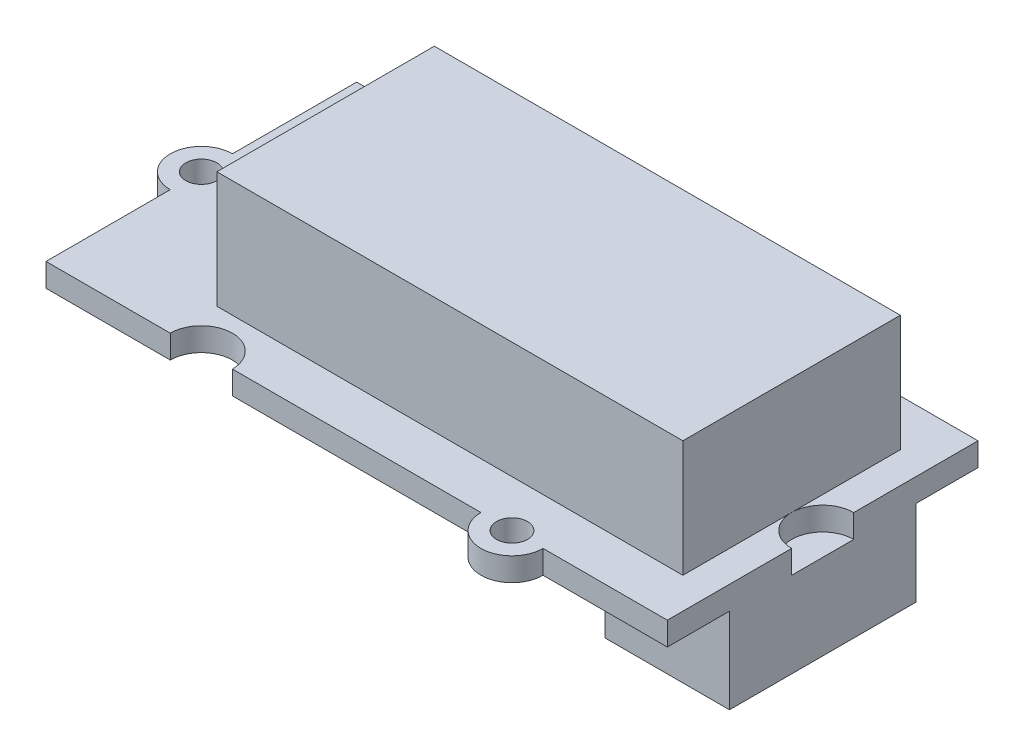
SolidWorks part; units mm, degrees
ref_plane "Спереди" through (0, 0, 0) normal (0, 0, 1) x (1, 0, 0)
ref_plane "Сверху" through (0, 0, 0) normal (0, 1, 0) x (1, 0, 0)
ref_plane "Справа" through (0, 0, 0) normal (1, 0, 0) x (0, 0, -1)
sketch "Эскиз1" plane through (0, 0, 0) normal (0, 1, 0) x (1, 0, 0)
  line L0 (-1000, 0) -> (49000, 0) construction
  line L1 (-20, 10) -> (-12, 10)
  line L2 (-20, 10) -> (-20, 2)
  line L3 (-20, -10) -> (-12, -10)
  line L4 (20, 10) -> (20, 2)
  line L5 (-20, 10) -> (20, -10) construction
  line L6 (-20, -10) -> (20, 10) construction
  line L7 (-8, -10) -> (8, -10) construction
  line L8 (-10, -10) -> (-10, 10) construction
  line L9 (-8, 10) -> (8, 10) construction
  line L10 (10, -10) -> (10, 10) construction
  line L11 (-20, -2) -> (-20, -10)
  line L12 (-8, -10) -> (8, -10)
  line L13 (-8, 10) -> (8, 10)
  line L14 (20, -2) -> (20, -10)
  line L17 (12, -10) -> (20, -10)
  line L18 (12, 10) -> (20, 10)
  circle A0 centre (-20, 0) radius 1
  arc A1 (-20, 2) -> (-20, -2) centre (-20, 0) ccw
  arc A2 (20, 2) -> (20, -2) centre (20, 0) ccw
  arc A3 (12, 10) -> (8, 10) centre (10, 10) ccw
  arc A4 (8, -10) -> (12, -10) centre (10, -10) ccw
  arc A5 (-12, 10) -> (-8, 10) centre (-10, 10) ccw
  arc A6 (-8, -10) -> (-12, -10) centre (-10, -10) ccw
  circle A7 centre (10, 10) radius 1
  circle A8 centre (10, -10) radius 1
  point P0 (0, 0)
  point P23 (0, 0)
  point P25 (0, 0)
  point P26 (0, 0)
  point P30 (0, 0)
  point P31 (0, 0)
  point P33 (0, 0)
  dimension "D3" = 4
  dimension "D4" = 2
  dimension "D5" = 4
  dimension "D1" = 40
  dimension "D2" = 20
  dimension "D6" = 10
  dimension "D7" = 10
extrude "Бобышка-Вытянуть1" add sketch "Эскиз1" along normal blind 1.5
sketch "Эскиз2" plane through (0, 1.5, 0) normal (0, 1, 0) x (1, 0, 0)
  line L1 (18, 7) -> (-12, 7)
  line L2 (18, 7) -> (18, -7)
  line L3 (18, -7) -> (-12, -7)
  line L4 (-12, 7) -> (-12, -7)
  arc A0 (20, 2) -> (20, -2) centre (20, 0) ccw construction
  point P4 (18, 0)
  dimension "D1" = 14
  dimension "D2" = 30
extrude "Бобышка-Вытянуть2" add sketch "Эскиз2" along normal blind 7.5
sketch "Эскиз3" plane through (0, 0, 0) normal (0, -1, 0) x (1, 0, 0)
  line L0 (20, -2) -> (20, -10) construction
  line L1 (12, 6) -> (20, 6)
  line L2 (12, 6) -> (12, -6)
  line L3 (12, -6) -> (20, -6)
  line L4 (20, 6) -> (20, -6)
  line L5 (18, 0) -> (4.8177, 0) construction
  point P6 (20, 0)
  point P12 (12, 0)
  dimension "D1" = 8
  dimension "D2" = 12
extrude "Бобышка-Вытянуть3" add sketch "Эскиз3" along normal blind 5.5
